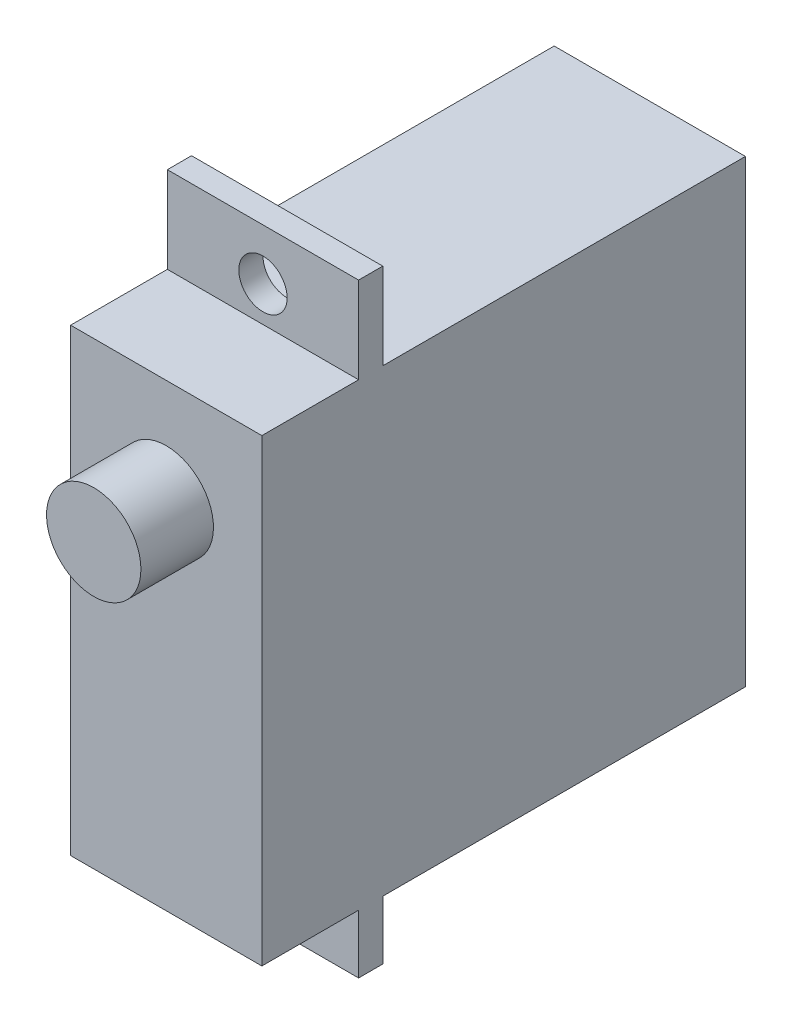
SolidWorks part; units mm, degrees
ref_plane "前视基准面" through (0, 0, 0) normal (0, 0, 1) x (1, 0, 0)
ref_plane "上视基准面" through (0, 0, 0) normal (0, 1, 0) x (1, 0, 0)
ref_plane "右视基准面" through (0, 0, 0) normal (1, 0, 0) x (0, 0, -1)
sketch "Sketch1" plane through (0, 0, 0) normal (1, 0, 0) x (0, 0, -1)
  line L1 (-17.96, 15.6242) -> (2.04, 15.6242)
  line L2 (-17.96, 15.6242) -> (-17.96, -3.3758)
  line L3 (-17.96, -3.3758) -> (2.04, -3.3758)
  line L4 (2.04, 15.6242) -> (2.04, -3.3758)
  line L5 (-17.96, 15.6242) -> (2.04, -3.3758) construction
  line L6 (-17.96, -3.3758) -> (2.04, 15.6242) construction
  point P0 (-7.96, 6.1242)
  dimension "D1" = 20
  dimension "D2" = 19
extrude "Boss-Extrude1" add sketch "Sketch1" along normal blind 7.91
sketch "Sketch2" plane through (7.91, 0, 0) normal (1, 0, 0) x (0, 0, -1)
  line L0 (2.04, -3.3758) -> (2.04, 15.6242) construction
  line L1 (-13.96, 19.1945) -> (-12.96, 19.1945)
  line L2 (-13.96, 19.1945) -> (-13.96, -5.8055)
  line L3 (-13.96, -5.8055) -> (-12.96, -5.8055)
  line L4 (-12.96, 19.1945) -> (-12.96, -5.8055)
  dimension "D2" = 1
  dimension "15" = 15
  dimension "D3" = 25
extrude "Boss-Extrude2" add sketch "Sketch2" against normal up to surface (7.91 mm away) contours L1 L4 L3 L2 up to face at (0, 6.1242, 7.96)
sketch "Sketch3" plane through (0, 0, 13.96) normal (0, 0, 1) x (1, 0, 0)
  line L0 (0, 15.6242) -> (0, -3.3758) construction
  line L1 (-3.955, -4.8308) -> (3.955, -4.8308) construction
  line L2 (-3.955, -4.8308) -> (-3.955, 17.0792) construction
  line L3 (-3.955, 17.0792) -> (3.955, 17.0792) construction
  line L4 (3.955, -4.8308) -> (3.955, 17.0792) construction
  line L5 (-3.955, -4.8308) -> (3.955, 17.0792) construction
  line L6 (-3.955, 17.0792) -> (3.955, -4.8308) construction
  circle A0 centre (3.955, 17.0792) radius 1
  circle A1 centre (3.955, -4.8308) radius 1
  point P0 (0, 6.1242)
  dimension "D1" = 21.91
extrude "Cut-Extrude1" cut sketch "Sketch3" against normal blind 21.9
sketch "Sketch4" plane through (0, 0, 17.96) normal (0, 0, 1) x (1, 0, 0)
  circle A0 centre (3.955, 11.3332) radius 1.9516
extrude "Boss-Extrude3" add sketch "Sketch4" along normal blind 3
equation "\"16。8\"=83.7992"
